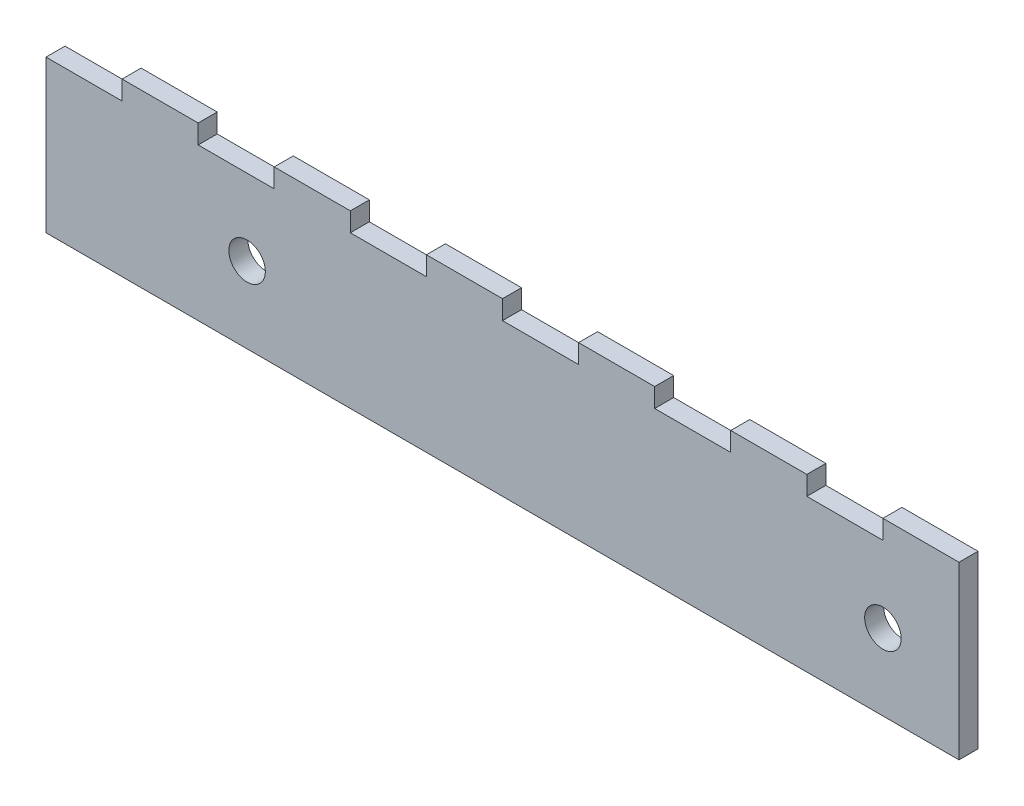
SolidWorks part; units mm, degrees
ref_plane "Front" through (0, 0, 0) normal (0, 0, 1) x (1, 0, 0)
ref_plane "Top" through (0, 0, 0) normal (0, 1, 0) x (1, 0, 0)
ref_plane "Right" through (0, 0, 0) normal (1, 0, 0) x (0, 0, -1)
sketch "Sketch1" plane through (0, 0, 0) normal (0, 0, 1) x (1, 0, 0)
  line L5 (0, 0) -> (152.4, 0)
  line L6 (0, 0) -> (0, 25.4)
  line L7 (0, 25.4) -> (152.4, 25.4)
  line L8 (152.4, 0) -> (152.4, 25.4)
  circle A0 centre (139.7, 12.7) radius 3.048
  circle A1 centre (33.5636, 12.7) radius 3.048
  circle A2 centre (-9.6164, 12.7) radius 3.048 construction
  point P4 (-30.8876, 13.2089)
  dimension "D7" = 6.096
  dimension "D8" = 6.096
  dimension "D9" = 6.096
  dimension "D1" = 152.4
  dimension "D2" = 25.4
  dimension "D3" = 43.18
  dimension "D4" = 106.1364
  dimension "D5" = 12.7
  dimension "D6" = 12.7
extrude "Boss-Extrude1" add sketch "Sketch1" along normal blind 3.175
sketch "Sketch3" plane through (0, 25.4, 0) normal (0, 1, 0) x (1, 0, 0)
  line L0 (152.4, -3.175) -> (0, -3.175) construction
  line L1 (152.4, 0) -> (139.7, 0)
  line L2 (152.4, 0) -> (152.4, -3.175)
  line L3 (152.4, -3.175) -> (139.7, -3.175)
  line L4 (139.7, 0) -> (139.7, -3.175)
  line L5 (127, 0) -> (127, -3.175)
  line L6 (127, 0) -> (114.3, 0)
  line L7 (114.3, 0) -> (114.3, -3.175)
  line L8 (127, -3.175) -> (114.3, -3.175)
  line L9 (101.6, 0) -> (101.6, -3.175)
  line L10 (101.6, 0) -> (88.9, 0)
  line L11 (88.9, 0) -> (88.9, -3.175)
  line L12 (101.6, -3.175) -> (88.9, -3.175)
  line L13 (76.2, 0) -> (76.2, -3.175)
  line L14 (76.2, 0) -> (63.5, 0)
  line L15 (63.5, 0) -> (63.5, -3.175)
  line L16 (76.2, -3.175) -> (63.5, -3.175)
  line L17 (50.8, 0) -> (50.8, -3.175)
  line L18 (50.8, 0) -> (38.1, 0)
  line L19 (38.1, 0) -> (38.1, -3.175)
  line L20 (50.8, -3.175) -> (38.1, -3.175)
  line L21 (25.4, 0) -> (25.4, -3.175)
  line L22 (25.4, 0) -> (12.7, 0)
  line L23 (12.7, 0) -> (12.7, -3.175)
  line L24 (25.4, -3.175) -> (12.7, -3.175)
  dimension "D1" = 12.7
  dimension "D2" = 6
extrude "Boss-Extrude3" add sketch "Sketch3" along normal blind 3.175
